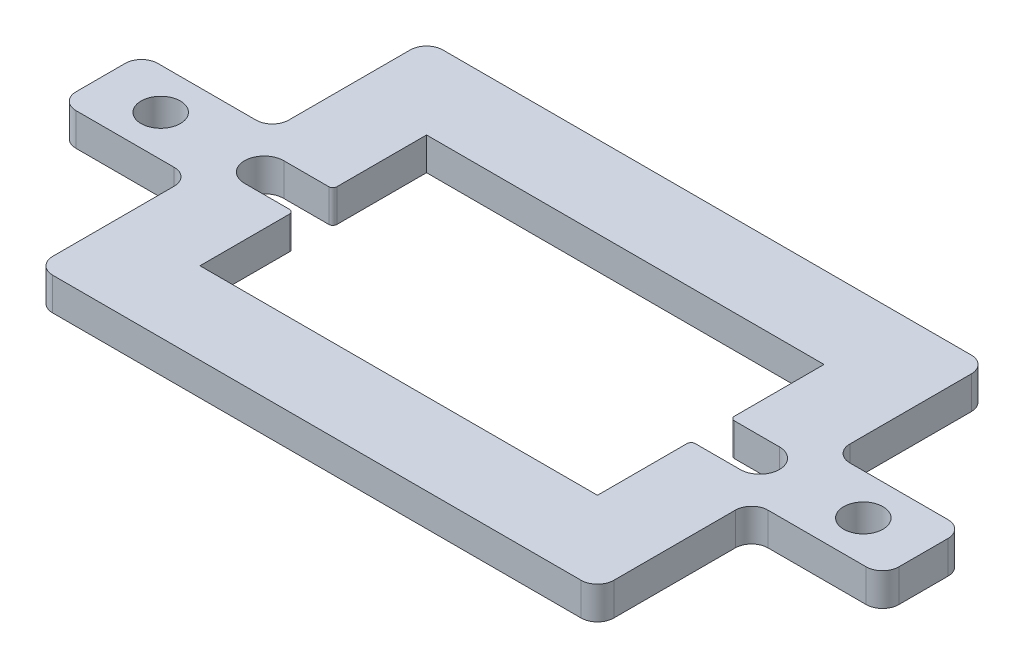
SolidWorks part; units mm, degrees
material "PLA"
ref_plane "Front Plane" through (0, 0, 0) normal (0, 0, 1) x (1, 0, 0)
ref_plane "Top Plane" through (0, 0, 0) normal (0, 1, 0) x (1, 0, 0)
ref_plane "Right Plane" through (0, 0, 0) normal (1, 0, 0) x (0, 0, -1)
sketch "Sketch1" plane through (0, 0, 0) normal (0, 1, 0) x (1, 0, 0)
  line L0 (-12.15, 6.925) -> (12.15, 6.925)
  line L1 (-11.4, 6.175) -> (11.4, 6.175) construction
  line L2 (-11.4, 6.175) -> (-11.4, -6.175) construction
  line L3 (-11.4, -6.175) -> (11.4, -6.175) construction
  line L4 (11.4, 6.175) -> (11.4, -6.175) construction
  line L5 (-11.4, 6.175) -> (11.4, -6.175) construction
  line L6 (-11.4, -6.175) -> (11.4, 6.175) construction
  line L7 (12.15, 6.925) -> (12.15, -6.925)
  line L8 (-12.15, -6.925) -> (12.15, -6.925)
  line L9 (-12.15, 6.925) -> (-12.15, -6.925)
  line L10 (-17.15, 11.925) -> (17.15, 11.925)
  line L11 (17.15, 11.925) -> (17.15, -11.925)
  line L12 (-17.15, -11.925) -> (17.15, -11.925)
  line L13 (-17.15, 11.925) -> (-17.15, -11.925)
  point P0 (0, 0)
  dimension "D1" = 22.8
  dimension "D2" = 12.35
  dimension "D3" = 0.75
  dimension "D4" = 5
extrude "Boss-Extrude1" add sketch "Sketch1" along normal blind 2
sketch "Sketch4" plane through (0, 2, 0) normal (0, 1, 0) x (1, 0, 0)
  line L0 (-17.15, 11.925) -> (-17.15, -11.925) construction
  line L1 (-17.15, 2.5) -> (-25.15, 2.5)
  line L2 (-17.15, 2.5) -> (-17.15, -2.5)
  line L3 (-17.15, -2.5) -> (-25.15, -2.5)
  line L4 (-25.15, 2.5) -> (-25.15, -2.5)
  line L5 (17.15, -11.925) -> (17.15, 11.925) construction
  line L6 (17.15, 2.5) -> (25.15, 2.5)
  line L7 (17.15, 2.5) -> (17.15, -2.5)
  line L8 (17.15, -2.5) -> (25.15, -2.5)
  line L9 (25.15, 2.5) -> (25.15, -2.5)
  point P12 (-25.15, 0)
  point P14 (25.15, 0)
  dimension "D1" = 5
  dimension "D2" = 8
extrude "Boss-Extrude2" add sketch "Sketch4" against normal up to surface (2 mm away) up to face at (0, 0, 0)
hole_wizard "M2 Clearance Hole1" positions "Sketch2" profile "Sketch3" hole size "M2" standard "ANSI Metric" end condition through all
sketch "Sketch2" plane through (0, 2, 0) normal (0, 1, 0) x (1, 0, 0)
  line L0 (-12.15, 6.925) -> (-12.15, -6.925) construction
  line L1 (12.15, -6.925) -> (12.15, 6.925) construction
  point P0 (-13.975, 0)
  point P2 (13.975, 0)
  point P11 (-21.475, 0)
  point P13 (21.475, 0)
  dimension "D1" = 1.825
  dimension "D2" = 1.825
  dimension "D3" = 7.5
  dimension "D4" = 7.5
sketch "Sketch3" plane through (-13.975, 2, 0) normal (1, 0, 0) x (0, 0, 1)
  line L0 (0, 0) -> (0, 2)
  line L1 (0, 2) -> (1.2, 2)
  line L2 (1.2, 2) -> (1.2, 0)
  line L5 (1.2, 0) -> (0, 0)
  line L11 (0, -6.35) -> (0, 107.95) construction
  dimension "Thru Hole Dia." = 2.4
  dimension "Thru Hole Depth" = 2
fillet "Fillet1" radius 1 12 edges at (17.15, 1, -11.925) (25.15, 1, -2.5) (17.15, 1, -2.5) (25.15, 1, 2.5) (17.15, 1, 2.5) (17.15, 1, 11.925) (-17.15, 1, 11.925) (-17.15, 1, -11.925) (-17.15, 1, -2.5) (-25.15, 1, -2.5) (-25.15, 1, 2.5) (-17.15, 1, 2.5)
sketch "Sketch5" plane through (0, 2, 0) normal (0, 1, 0) x (1, 0, 0)
  line L0 (-12.15, 1.2) -> (-15.15, 1.2)
  line L3 (-12.15, 6.925) -> (-12.15, -6.925) construction
  line L4 (-15.15, -1.2) -> (-12.15, -1.2)
  line L7 (-12.15, 1.2) -> (-12.15, -1.2)
  line L8 (0, 0) -> (0, -3.4547) construction
  line L9 (12.15, 1.2) -> (15.15, 1.2)
  line L10 (15.15, -1.2) -> (12.15, -1.2)
  line L11 (12.15, 1.2) -> (12.15, -1.2)
  arc A5 (-15.15, 1.2) -> (-15.15, -1.2) centre (-15.15, 0) ccw
  circle A6 centre (-13.975, 0) radius 1.2 construction
  arc A7 (15.15, 1.2) -> (15.15, -1.2) centre (15.15, 0) cw
  dimension "D1" = 3
extrude "Cut-Extrude1" cut sketch "Sketch5" against normal through all
fillet "Fillet2" radius 0.25 4 edges at (12.15, 1, 1.2) (12.15, 1, -1.2) (-12.15, 1, 1.2) (-12.15, 1, -1.2)
